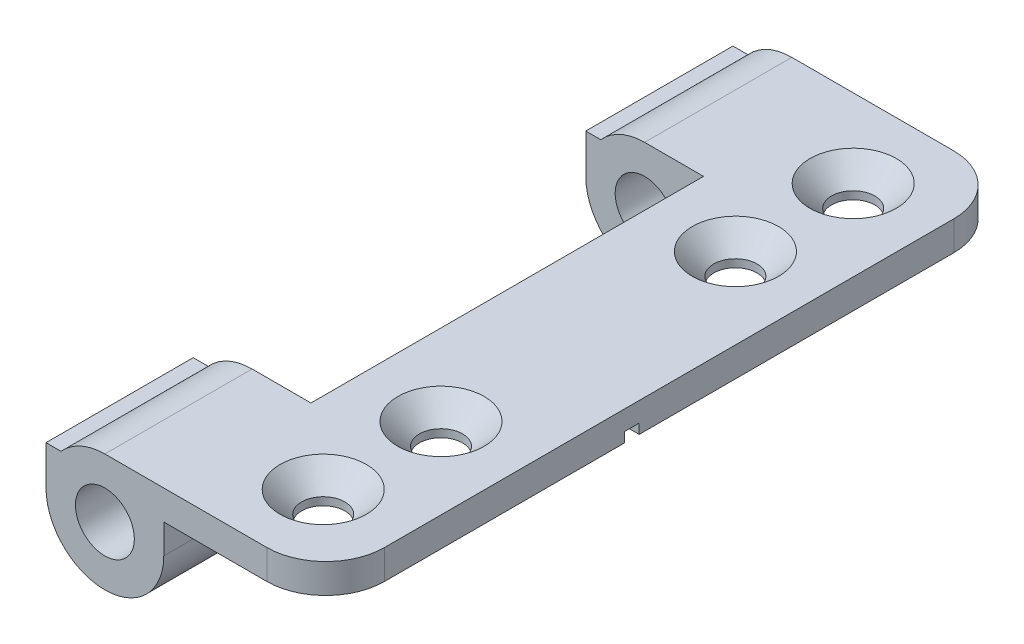
SolidWorks part; units mm, degrees
ref_plane "Front Plane" through (0, 0, 0) normal (0, 0, 1) x (1, 0, 0)
ref_plane "Top Plane" through (0, 0, 0) normal (0, 1, 0) x (1, 0, 0)
ref_plane "Right Plane" through (0, 0, 0) normal (1, 0, 0) x (0, 0, -1)
sketch "Sketch2" plane through (0, 0, 0) normal (0, 0, 1) x (1, 0, 0)
  line L0 (3, 3) -> (11.25, 3)
  line L1 (11.25, 3) -> (11.25, 1.5)
  line L2 (11.25, 1.5) -> (3, 1.5)
  line L3 (0, 1.5) -> (15.0271, 1.5) construction
  line L6 (3, 0) -> (3, 1.5)
  line L7 (-3, 0) -> (-3, 2)
  line L8 (-3, 2) -> (-2.2361, 2)
  line L10 (0, 3) -> (3, 3)
  circle A0 centre (0, 0) radius 1.5
  arc A2 (-3, 0) -> (3, 0) centre (0, 0) ccw
  arc A3 (0, 3) -> (-2.2361, 2) centre (0, 0) ccw
  arc A4 (-3, 0) -> (-2.9648, 0.4584) centre (0, 0) ccw construction
  dimension "D1" = 3
  dimension "D2" = 1.5
  dimension "D3" = 1.5
  dimension "D4" = 8.25
  dimension "D6" = 0.5
extrude "Boss-Extrude1" add sketch "Sketch2" along normal blind 7.5
sketch "Sketch4" plane through (0, 0, 7.5) normal (0, 0, 1) x (1, 0, 0)
  line L1 (11.25, 3) -> (3, 3)
  line L2 (11.25, 3) -> (11.25, 1.5)
  line L3 (11.25, 1.5) -> (3, 1.5)
  line L4 (3, 3) -> (3, 1.5)
  line L5 (11.25, 3) -> (3, 1.5) construction
  line L6 (11.25, 1.5) -> (3, 3) construction
  point P4 (7.125, 2.25)
extrude "Boss-Extrude3" add sketch "Sketch4" along normal blind 20
sketch "Sketch5" plane through (0, 0, 27.5) normal (0, 0, 1) x (1, 0, 0)
  line L38 (11.25, 1.5) -> (11.25, 3) construction
  line L39 (11.25, 3) -> (3, 3) construction
  line L41 (3, 1.5) -> (11.25, 1.5) construction
  line L45 (3, 3) -> (0, 3) construction
  line L53 (-2.2361, 2) -> (-3, 2) construction
  line L54 (-3, 2) -> (-3, 0) construction
  line L55 (3, 0) -> (3, 1.5) construction
  line L56 (11.25, 1.5) -> (11.25, 3)
  line L57 (11.25, 3) -> (3, 3)
  line L59 (3, 1.5) -> (11.25, 1.5)
  line L61 (3, 3) -> (0, 3)
  line L62 (-2.2361, 2) -> (-3, 2)
  line L63 (-3, 2) -> (-3, 0)
  line L64 (3, 0) -> (3, 1.5)
  arc A12 (0, 3) -> (-2.2361, 2) centre (0, 0) ccw construction
  arc A13 (-3, 0) -> (3, 0) centre (0, 0) ccw construction
  arc A18 (0, 3) -> (-2.2361, 2) centre (0, 0) ccw
  arc A19 (-3, 0) -> (3, 0) centre (0, 0) ccw
  circle A20 centre (0, 0) radius 1.5 construction
  circle A21 centre (0, 0) radius 1.5
extrude "Boss-Extrude4" add sketch "Sketch5" along normal blind 7.5
sketch "Sketch6" plane through (3, 0, 0) normal (-1, 0, 0) x (0, 0, 1)
  line L7 (27.5, 1.5) -> (7.5, 1.5) construction
  line L8 (19.025, 1.5) -> (19.775, 1.5)
  line L9 (19.025, 1.5) -> (19.025, 2)
  line L10 (19.025, 2) -> (19.775, 2)
  line L11 (19.775, 1.5) -> (19.775, 2)
  line L12 (19.025, 1.5) -> (19.775, 2) construction
  line L13 (19.025, 2) -> (19.775, 1.5) construction
  point P12 (19.4, 1.75)
  dimension "D1" = 7.725
  dimension "D5" = 0.75
  dimension "D6" = 0.5
extrude "Cut-Extrude1" cut sketch "Sketch6" against normal through all
sketch "Sketch7" plane through (0, 1.5, 0) normal (0, -1, 0) x (1, 0, 0)
  line L0 (7.125, 0) -> (7.125, 35) construction
  line L6 (3, 0) -> (11.25, 0) construction
  line L7 (3, 35) -> (11.25, 35) construction
  circle A0 centre (7.125, 25) radius 1.1
  circle A1 centre (7.125, 10) radius 1.1
  circle A2 centre (7.125, 31) radius 1.1
  circle A3 centre (7.125, 4) radius 1.1
  dimension "D6" = 2.2
  dimension "D2" = 15
  dimension "D3" = 6
  dimension "D4" = 6
  dimension "D1" = 35
  dimension "D5" = 10
extrude "Cut-Extrude2" cut sketch "Sketch7" against normal through all
chamfer "Chamfer1" distance 1.1 angle 45 4 edges at (8.225, 3, 31) (8.225, 3, 25) (8.225, 3, 10) (8.225, 3, 4)
fillet "Fillet1" radius 3 2 edges at (11.25, 2.25, 0) (11.25, 2.25, 35)
equation "\"D4@Sketch7\"=\"D3@Sketch7\""
equation "\"D5@Sketch7\"=(\"D1@Sketch7\"-\"D2@Sketch7\")/2"
